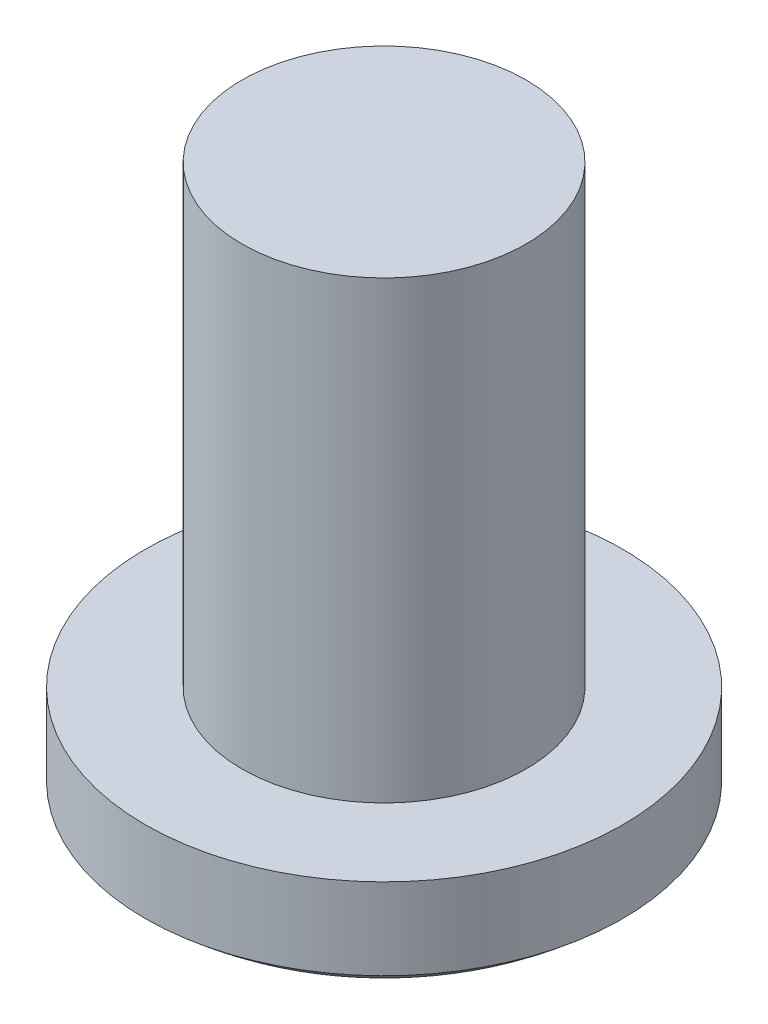
SolidWorks part; units mm, degrees
ref_plane "Front" through (0, 0, 0) normal (0, 0, 1) x (1, 0, 0)
ref_plane "Top" through (0, 0, 0) normal (0, 1, 0) x (1, 0, 0)
ref_plane "Right" through (0, 0, 0) normal (1, 0, 0) x (0, 0, -1)
sketch "草图1" plane through (0, 0, 0) normal (0, 1, 0) x (1, 0, 0)
  circle A0 centre (0, 0) radius 4.2
  dimension "D1" = 8.4
extrude "凸台-拉伸1" add sketch "草图1" along normal blind 2.9
sketch "草图2" plane through (0, 2.9, 0) normal (0, 1, 0) x (1, 0, 0)
  circle A0 centre (0, 0) radius 2.5
  dimension "D1" = 5
extrude "凸台-拉伸2" add sketch "草图2" along normal blind 8
sketch "草图3" plane through (0, 0, 0) normal (1, 0, 0) x (0, 0, -1)
  line L0 (-4.2, 1.4695) -> (-5.1009, -0.9525)
  line L2 (0, 1.0359) -> (0, -1.9035) construction
  line L3 (-5.1009, -0.9525) -> (5.4547, -0.9525)
  line L4 (5.4547, -0.9525) -> (4.2, 1.9884)
  line L5 (4.2, 0) -> (4.2, 2.9) construction
  line L6 (-4.2, 2.9) -> (-4.2, 0) construction
  arc A0 (-4.2, 1.4695) -> (4.2, 1.9884) centre (-0.2629, 5.9854) ccw
  point P1 (-0.2629, 5.9854)
  point P13 (-5.1303, -1.0314)
  point P14 (5.4547, -0.9525)
ref_plane "基准面1" through (0, -5, 0) normal (0, 1, 0) x (1, 0, 0)
revolve "切除-旋转1" cut sketch "草图3" angle 360 about L2
sketch "草图4" plane through (0, -5, 0) normal (0, 1, 0) x (1, 0, 0)
  line L0 (-2.5, 0) -> (2.5, 0) construction
  line L1 (0, -2.5) -> (0, 2.5) construction
  line L2 (0.4, -2.5) -> (0.4, -0.4)
  line L3 (-2.5, -0.4) -> (-0.4, -0.4)
  line L4 (-0.4, -2.5) -> (-0.4, -0.4)
  line L5 (-2.5, 0.4) -> (-0.4, 0.4)
  line L6 (0.4, -2.5) -> (-0.4, -2.5)
  line L7 (0.4, 2.5) -> (-0.4, 2.5)
  line L8 (-2.5, -0.4) -> (-2.5, 0.4)
  line L9 (2.5, -0.4) -> (2.5, 0.4)
  line L10 (-0.4, 0.4) -> (-0.4, 2.5)
  line L11 (0.4, 0.4) -> (2.5, 0.4)
  line L12 (-0.4, -2.5) -> (-0.4, 2.5) construction
  line L13 (0.4, 0.4) -> (0.4, 2.5)
  line L14 (-2.5, 0.4) -> (2.5, 0.4) construction
  line L15 (0.4, -0.4) -> (2.5, -0.4)
  line L16 (0.4, -2.5) -> (0.4, 2.5) construction
  line L18 (-2.5, -0.4) -> (2.5, -0.4) construction
  dimension "D1" = 2.5
  dimension "D2" = 2.5
  dimension "D3" = 2.5
  dimension "D4" = 2.5
  dimension "D5" = 0.4
  dimension "D6" = 0.4
extrude "切除-拉伸1" cut sketch "草图4" along normal offset from surface (6.4 mm away) 1.5 up to face at (0, 2.9, 2.5)
